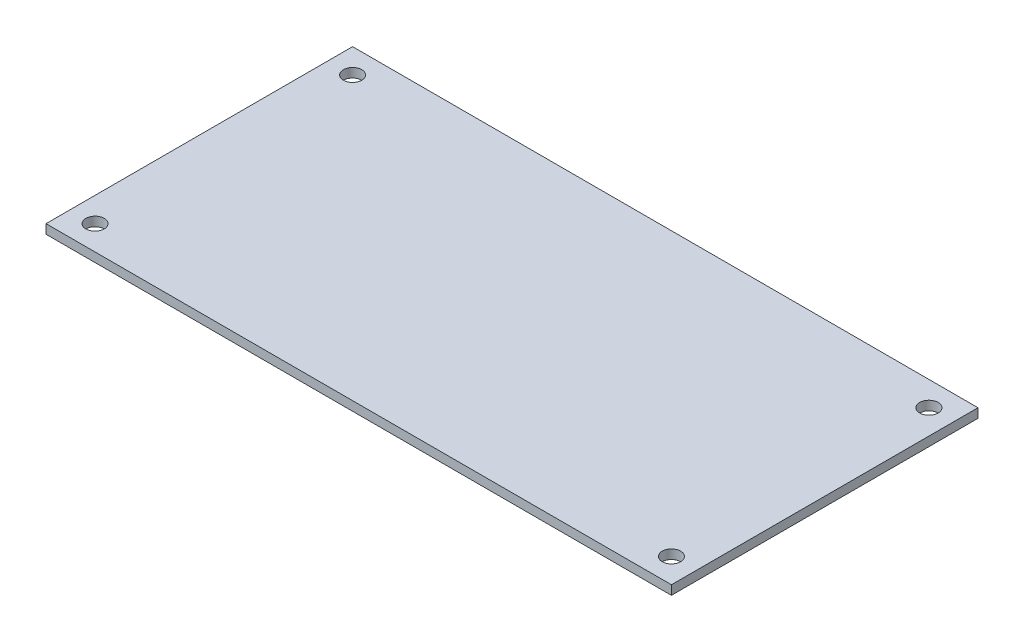
SolidWorks part; units mm, degrees
material "PVC Rigid"
ref_plane "Front Plane" through (0, 0, 0) normal (0, 0, 1) x (1, 0, 0)
ref_plane "Top Plane" through (0, 0, 0) normal (0, 1, 0) x (1, 0, 0)
ref_plane "Right Plane" through (0, 0, 0) normal (1, 0, 0) x (0, 0, -1)
sketch "Sketch1" plane through (0, 0, 0) normal (0, 1, 0) x (1, 0, 0)
  line L0 (0, 31.3748) -> (0, -31.6719) construction
  line L1 (-51, -25) -> (51, -25)
  line L2 (-51, -25) -> (-51, 25)
  line L3 (-51, 25) -> (51, 25)
  line L4 (51, -25) -> (51, 25)
  line L5 (-51, -25) -> (51, 25) construction
  line L6 (-51, 25) -> (51, -25) construction
  line L7 (-60.4578, 0) -> (58.8582, 0) construction
  line L8 (-51, -7) -> (51, -7) construction
  circle A0 centre (-47, 21) radius 1.5
  circle A1 centre (47, 21) radius 1.5
  circle A2 centre (47, -21) radius 1.5
  circle A3 centre (-47, -21) radius 1.5
  point P0 (0, 0)
  dimension "D5" = 3
  dimension "D6" = 18
  dimension "D1" = 102
  dimension "D2" = 50
  dimension "D3" = 4
  dimension "D4" = 4
extrude "Boss-Extrude1" add sketch "Sketch1" along normal blind 1.5
